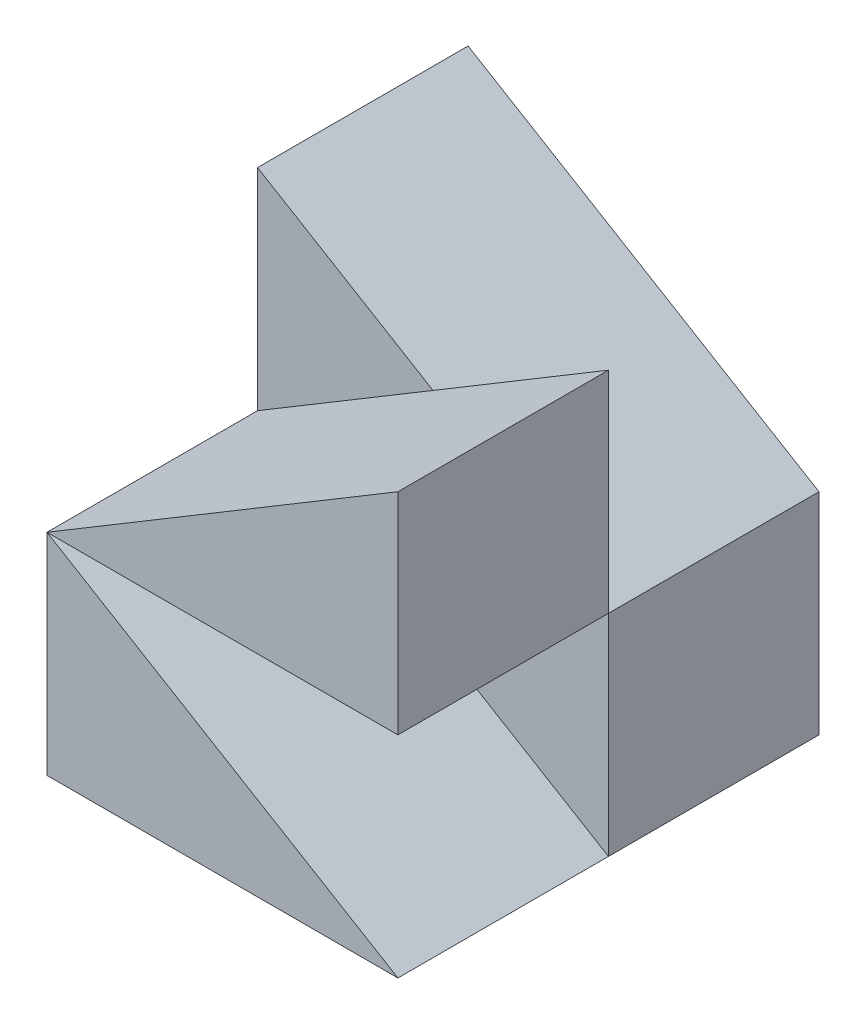
SolidWorks part; units mm, degrees
ref_plane "Front Plane" through (0, 0, 0) normal (0, 0, 1) x (1, 0, 0)
ref_plane "Top Plane" through (0, 0, 0) normal (0, 1, 0) x (1, 0, 0)
ref_plane "Right Plane" through (0, 0, 0) normal (1, 0, 0) x (0, 0, -1)
sketch "Sketch1" plane through (0, 0, 0) normal (0, 0, 1) x (1, 0, 0)
  line L0 (-25, 0) -> (0, 15)
  line L1 (0, 15) -> (0, 0)
  line L2 (0, 0) -> (-25, 0)
  dimension "D1" = 25
  dimension "D2" = 15
extrude "Boss-Extrude1" add sketch "Sketch1" along normal blind 15
sketch "Sketch2" plane through (0, 0, 0) normal (0, 0, -1) x (-1, 0, 0)
  line L0 (0, 15) -> (25.0005, 15)
  line L1 (25.0005, 15) -> (25.0005, 30)
  line L2 (25.0005, 30) -> (0, 15)
  dimension "D1" = 25.0005
  dimension "D2" = 15
extrude "Boss-Extrude2" add sketch "Sketch2" against normal blind 15 separate body
sketch "Sketch3" plane through (0, 0, 15) normal (0, 0, 1) x (1, 0, 0)
  line L0 (0, 0) -> (-25, 0)
  line L1 (-25, 0) -> (-25, 15)
  line L2 (-25, 15) -> (0, 0)
  dimension "D1" = 15
extrude "Boss-Extrude3" add sketch "Sketch3" along normal blind 15
sketch "Sketch4" plane through (0, 0, 15) normal (0, 0, 1) x (1, 0, 0)
  line L0 (-25.0005, 15) -> (0, 15)
  line L1 (0, 15) -> (0, 30)
  line L2 (0, 30) -> (-25.0005, 15)
  dimension "D1" = 15
extrude "Boss-Extrude4" add sketch "Sketch4" along normal blind 15
